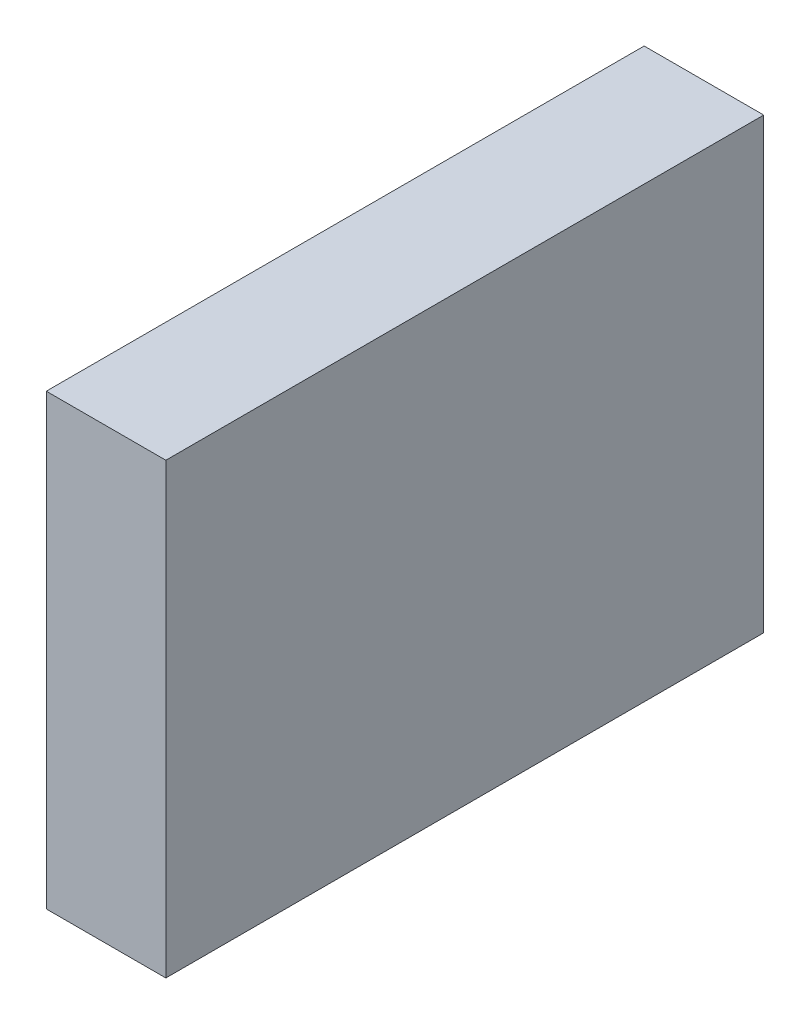
SolidWorks part; units mm, degrees
ref_plane "Front Plane" through (0, 0, 0) normal (0, 0, 1) x (1, 0, 0)
ref_plane "Top Plane" through (0, 0, 0) normal (0, 1, 0) x (1, 0, 0)
ref_plane "Right Plane" through (0, 0, 0) normal (1, 0, 0) x (0, 0, -1)
sketch "Sketch1" plane through (0, 0, 0) normal (0, 1, 0) x (1, 0, 0)
  line L1 (20, 100) -> (-20, 100)
  line L2 (20, 100) -> (20, -100)
  line L3 (20, -100) -> (-20, -100)
  line L4 (-20, 100) -> (-20, -100)
  line L5 (20, 100) -> (-20, -100) construction
  line L6 (20, -100) -> (-20, 100) construction
  point P0 (0, 0)
  dimension "D1" = 200
  dimension "D2" = 40
extrude "Boss-Extrude1" add sketch "Sketch1" along normal blind 150
